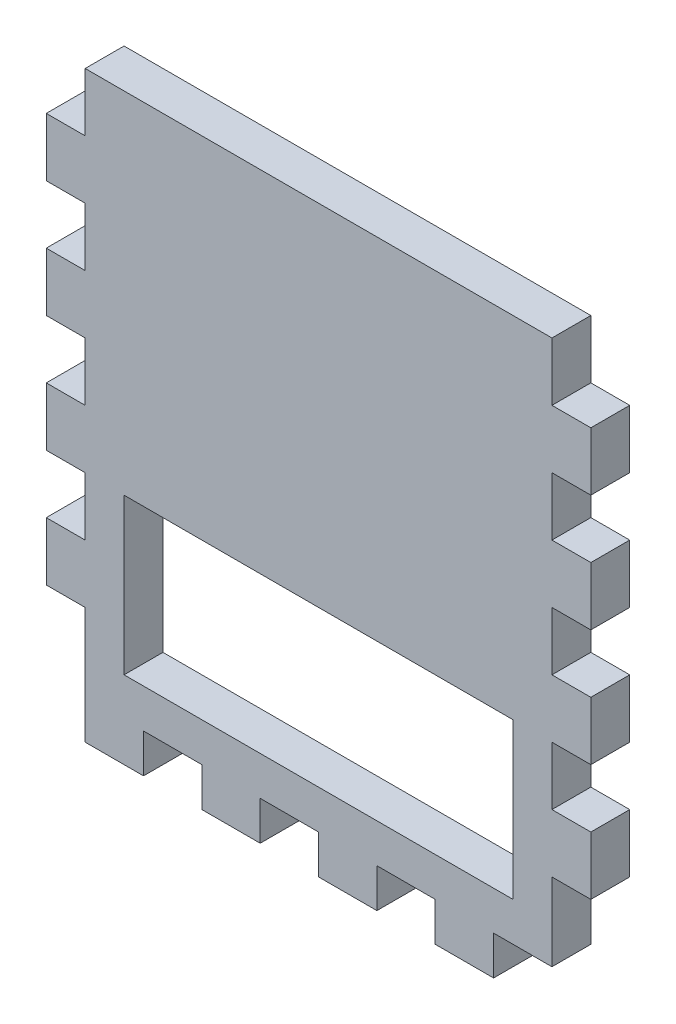
SolidWorks part; units mm, degrees
material "Pine"
ref_plane "Front Plane" through (0, 0, 0) normal (0, 0, 1) x (1, 0, 0)
ref_plane "Top Plane" through (0, 0, 0) normal (0, 1, 0) x (1, 0, 0)
ref_plane "Right Plane" through (0, 0, 0) normal (1, 0, 0) x (0, 0, -1)
sketch "Sketch1" plane through (0, 0, 0) normal (0, 0, 1) x (1, 0, 0)
  line L1 (0, 0) -> (76.2, 0)
  line L2 (0, 0) -> (0, -88.9)
  line L3 (0, -88.9) -> (76.2, -88.9)
  line L4 (76.2, 0) -> (76.2, -88.9)
  line L5 (6.35, -57.15) -> (69.85, -57.15)
  line L6 (6.35, -57.15) -> (6.35, -82.55)
  line L7 (6.35, -82.55) -> (69.85, -82.55)
  line L8 (69.85, -57.15) -> (69.85, -82.55)
  dimension "D1" = 88.9
  dimension "D2" = 76.2
  dimension "D4" = 25.4
  dimension "D5" = 63.5
  dimension "D8" = 6.35
  dimension "D9" = 6.35
extrude "Boss-Extrude1" add sketch "Sketch1" along normal blind 6.35
sketch "Sketch2" plane through (0, 0, 6.35) normal (0, 0, 1) x (1, 0, 0)
  line L0 (0, 0) -> (0, -88.9) construction
  line L1 (0, -9.525) -> (-6.35, -9.525)
  line L2 (0, -9.525) -> (0, -19.05)
  line L3 (0, -19.05) -> (-6.35, -19.05)
  line L4 (-6.35, -9.525) -> (-6.35, -19.05)
  line L5 (76.2, 0) -> (0, 0) construction
  line L6 (0, -28.575) -> (0, -38.1)
  line L7 (0, -28.575) -> (-6.35, -28.575)
  line L8 (-6.35, -28.575) -> (-6.35, -38.1)
  line L9 (0, -38.1) -> (-6.35, -38.1)
  line L10 (0, -47.625) -> (0, -57.15)
  line L11 (0, -47.625) -> (-6.35, -47.625)
  line L12 (-6.35, -47.625) -> (-6.35, -57.15)
  line L13 (0, -57.15) -> (-6.35, -57.15)
  line L14 (0, -66.675) -> (0, -76.2)
  line L15 (0, -66.675) -> (-6.35, -66.675)
  line L16 (-6.35, -66.675) -> (-6.35, -76.2)
  line L17 (0, -76.2) -> (-6.35, -76.2)
  line L23 (0, -88.9) -> (9.525, -88.9)
  line L24 (0, -88.9) -> (0, -95.25)
  line L25 (0, -95.25) -> (9.525, -95.25)
  line L26 (9.525, -88.9) -> (9.525, -95.25)
  line L39 (38.1, 0) -> (38.1, -88.9) construction
  line L57 (19.05, -88.9) -> (19.05, -95.25)
  line L58 (19.05, -88.9) -> (28.575, -88.9)
  line L59 (28.575, -88.9) -> (28.575, -95.25)
  line L60 (19.05, -95.25) -> (28.575, -95.25)
  line L76 (76.2, -66.675) -> (82.55, -66.675)
  line L77 (82.55, -66.675) -> (82.55, -76.2)
  line L78 (76.2, -76.2) -> (82.55, -76.2)
  line L79 (76.2, -66.675) -> (76.2, -76.2)
  line L80 (76.2, -47.625) -> (82.55, -47.625)
  line L81 (82.55, -47.625) -> (82.55, -57.15)
  line L82 (76.2, -57.15) -> (82.55, -57.15)
  line L83 (76.2, -47.625) -> (76.2, -57.15)
  line L84 (76.2, -28.575) -> (82.55, -28.575)
  line L85 (82.55, -28.575) -> (82.55, -38.1)
  line L86 (76.2, -38.1) -> (82.55, -38.1)
  line L87 (76.2, -28.575) -> (76.2, -38.1)
  line L88 (76.2, -19.05) -> (82.55, -19.05)
  line L89 (82.55, -9.525) -> (82.55, -19.05)
  line L90 (76.2, -9.525) -> (82.55, -9.525)
  line L91 (76.2, -9.525) -> (76.2, -19.05)
  line L104 (38.1, -88.9) -> (38.1, -95.25)
  line L105 (38.1, -88.9) -> (47.625, -88.9)
  line L106 (47.625, -88.9) -> (47.625, -95.25)
  line L107 (38.1, -95.25) -> (47.625, -95.25)
  line L108 (57.15, -88.9) -> (57.15, -95.25)
  line L109 (57.15, -88.9) -> (66.675, -88.9)
  line L110 (66.675, -88.9) -> (66.675, -95.25)
  line L111 (57.15, -95.25) -> (66.675, -95.25)
  line L112 (0, -88.9) -> (76.2, -88.9) construction
  point P29 (79.6896, -24.6781)
  point P56 (83.3019, -17.4533)
  point P57 (0, 0)
  point P58 (0, 0)
  dimension "D1" = 6.35
  dimension "D2" = 9.525
  dimension "D3" = 9.525
  dimension "D5" = 9.525
  dimension "D6" = 6.35
  dimension "D7" = 4
  dimension "D8" = 9.525
  dimension "D9" = 9.525
  dimension "D4" = 4
extrude "Boss-Extrude3" add sketch "Sketch2" against normal up to surface (6.35 mm away) up to face at (38.1, -44.45, 0)
